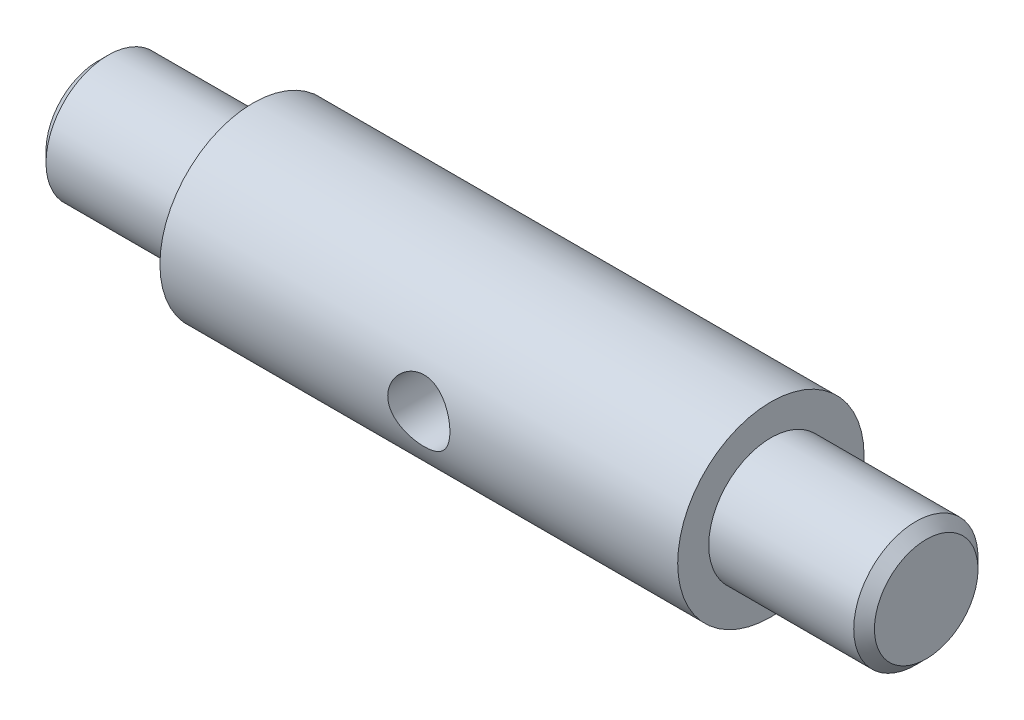
SolidWorks part; units mm, degrees
ref_plane "Front Plane" through (0, 0, 0) normal (0, 0, 1) x (1, 0, 0)
ref_plane "Top Plane" through (0, 0, 0) normal (0, 1, 0) x (1, 0, 0)
ref_plane "Right Plane" through (0, 0, 0) normal (1, 0, 0) x (0, 0, -1)
sketch "Sketch1" plane through (0, 0, 0) normal (0, 0, 1) x (1, 0, 0)
  line L0 (0, 0) -> (80, 0)
  line L1 (80, 0) -> (80, 6)
  line L2 (80, 6) -> (65, 6)
  line L3 (65, 6) -> (65, 9)
  line L4 (65, 9) -> (15, 9)
  line L5 (15, 9) -> (15, 6)
  line L6 (15, 6) -> (0, 6)
  line L7 (0, 6) -> (0, 0)
  dimension "D1" = 80
  dimension "D2" = 15
  dimension "D3" = 6
  dimension "D4" = 9
revolve "Revolve1" add sketch "Sketch1" angle 360 about L0
sketch "Sketch2" plane through (0, 0, 0) normal (0, 0, 1) x (1, 0, 0)
  line L0 (15, 6) -> (15, -6) construction
  circle A0 centre (40, 0) radius 3
  dimension "D1" = 6
  dimension "D2" = 25
extrude "Cut-Extrude1" cut sketch "Sketch2" against normal through all both and the other way through all
chamfer "Chamfer1" distance 1 angle 45 2 edges at (80, 0, 6) (0, 0, 6)
hole_wizard "Ø6.0 (6) Diameter Hole1" positions "Sketch3" profile "Sketch4" hole size "Ø6.0" standard "DIN"
sketch "Sketch3" plane through (0, 0, 0) normal (-1, 0, 0) x (0, 0, 1)
  point P0 (0, 0)
sketch "Sketch4" plane through (0, 0, 0) normal (0, 1, 0) x (0, 0, 1)
  line L0 (0, 0) -> (0, 46.8026)
  line L1 (0, 46.8026) -> (3, 45)
  line L2 (3, 45) -> (3, 0)
  line L5 (3, 0) -> (0, 0)
  line L10 (0, 46.8026) -> (-3, 45) construction
  line L11 (0, -6.35) -> (0, 107.95) construction
  dimension "Hole Dia." = 6
  dimension "Hole Depth" = 45
  dimension "Drill Angle" = 118
